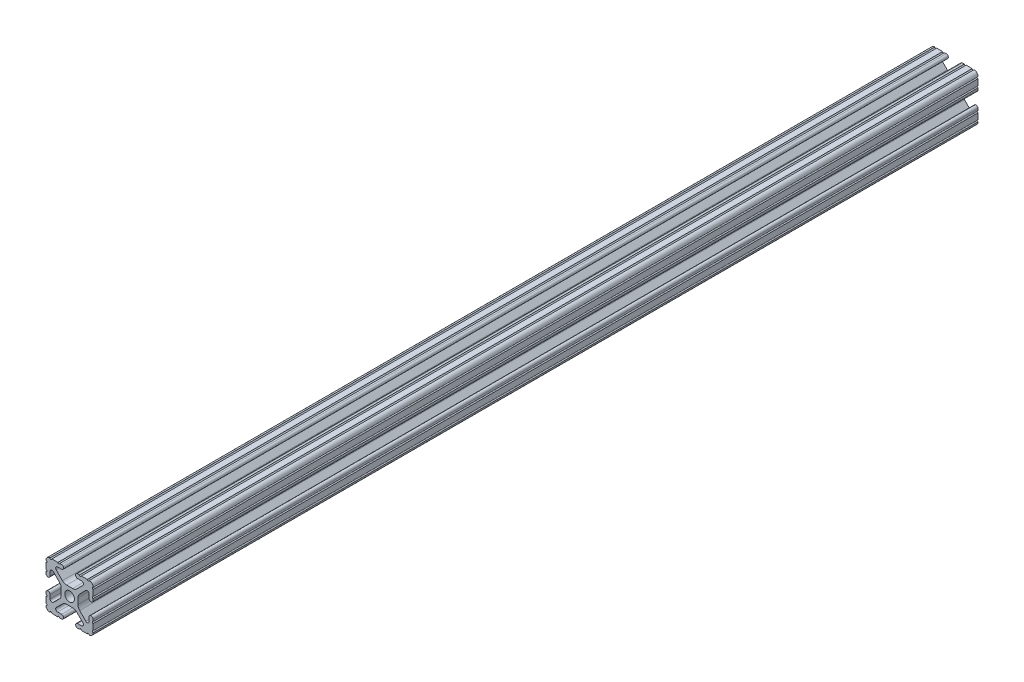
SolidWorks part; units mm, degrees
material "6061-T6 (SS)"
ref_plane "Front Plane" through (0, 0, 0) normal (0, 0, 1) x (1, 0, 0)
ref_plane "Top Plane" through (0, 0, 0) normal (0, 1, 0) x (1, 0, 0)
ref_plane "Right Plane" through (0, 0, 0) normal (1, 0, 0) x (0, 0, -1)
ref_plane "Plane1" through (0, 0, -450.85) normal (0, 0, -1) x (-1, 0, 0)
sketch "Sketch1" plane through (0, 0, -450.85) normal (0, 0, -1) x (-1, 0, 0)
  line L0 (12.7, -9.5504) -> (12.7, -6.3331)
  line L1 (12.7, -5.3171) -> (12.7, -4.3434)
  line L2 (10.4902, -4.3434) -> (10.4902, -6.4748)
  line L3 (8.7558, -7.1932) -> (5.4257, -3.8632)
  line L4 (4.4958, -1.6181) -> (4.4958, 1.6181)
  line L5 (5.4257, 3.8632) -> (8.7558, 7.1932)
  line L6 (10.4902, 6.4748) -> (10.4902, 4.3434)
  line L7 (12.7, 4.3434) -> (12.7, 5.3171)
  line L8 (12.7, 6.3331) -> (12.7, 9.5504)
  line L9 (9.5504, 12.7) -> (6.3331, 12.7)
  line L10 (5.3171, 12.7) -> (4.3434, 12.7)
  line L11 (4.3434, 10.4902) -> (6.4748, 10.4902)
  line L12 (7.1932, 8.7558) -> (3.8632, 5.4257)
  line L13 (1.6181, 4.4958) -> (-1.6181, 4.4958)
  line L14 (-3.8632, 5.4257) -> (-7.1932, 8.7558)
  line L15 (-6.4748, 10.4902) -> (-4.3434, 10.4902)
  line L16 (-4.3434, 12.7) -> (-5.3171, 12.7)
  line L17 (-6.3331, 12.7) -> (-9.5504, 12.7)
  line L18 (-12.7, 9.5504) -> (-12.7, 6.3331)
  line L19 (-12.7, 5.3171) -> (-12.7, 4.3434)
  line L20 (-10.4902, 4.3434) -> (-10.4902, 6.4748)
  line L21 (-8.7558, 7.1932) -> (-5.4257, 3.8632)
  line L22 (-4.4958, 1.6181) -> (-4.4958, -1.6181)
  line L23 (-5.4257, -3.8632) -> (-8.7558, -7.1932)
  line L24 (-10.4902, -6.4748) -> (-10.4902, -4.3434)
  line L25 (-12.7, -4.3434) -> (-12.7, -5.3171)
  line L26 (-12.7, -6.3331) -> (-12.7, -9.5504)
  line L27 (-9.5504, -12.7) -> (-6.3331, -12.7)
  line L28 (-5.3171, -12.7) -> (-4.3434, -12.7)
  line L29 (-4.3434, -10.4902) -> (-6.4748, -10.4902)
  line L30 (-7.1932, -8.7558) -> (-3.8632, -5.4257)
  line L31 (-1.6181, -4.4958) -> (1.6181, -4.4958)
  line L32 (3.8632, -5.4257) -> (7.1932, -8.7558)
  line L33 (6.4748, -10.4902) -> (4.3434, -10.4902)
  line L34 (4.3434, -12.7) -> (5.3171, -12.7)
  line L35 (6.3331, -12.7) -> (9.5504, -12.7)
  arc A0 (12.6998, -10.5664) -> (12.7, -9.5504) centre (12.7, -10.0584) cw
  arc A1 (12.7, -6.3331) -> (12.7, -5.3171) centre (12.7, -5.8251) cw
  arc A2 (12.7, -4.3434) -> (10.4902, -4.3434) centre (11.5951, -4.3434) ccw
  arc A3 (10.4902, -6.4748) -> (8.7558, -7.1932) centre (9.4742, -6.4748) cw
  arc A4 (5.4257, -3.8632) -> (4.4958, -1.6181) centre (7.6708, -1.6181) cw
  arc A5 (4.4958, 1.6181) -> (5.4257, 3.8632) centre (7.6708, 1.6181) cw
  arc A6 (8.7558, 7.1932) -> (10.4902, 6.4748) centre (9.4742, 6.4748) cw
  arc A7 (10.4902, 4.3434) -> (12.7, 4.3434) centre (11.5951, 4.3434) ccw
  arc A8 (12.7, 5.3171) -> (12.7, 6.3331) centre (12.7, 5.8251) cw
  arc A9 (12.7, 9.5504) -> (12.6998, 10.5664) centre (12.7, 10.0584) cw
  arc A10 (12.6998, 10.5664) -> (10.5664, 12.6998) centre (10.5918, 10.5918) ccw
  arc A11 (10.5664, 12.6998) -> (9.5504, 12.7) centre (10.0584, 12.7) cw
  arc A12 (6.3331, 12.7) -> (5.3171, 12.7) centre (5.8251, 12.7) cw
  arc A13 (4.3434, 12.7) -> (4.3434, 10.4902) centre (4.3434, 11.5951) ccw
  arc A14 (6.4748, 10.4902) -> (7.1932, 8.7558) centre (6.4748, 9.4742) cw
  arc A15 (3.8632, 5.4257) -> (1.6181, 4.4958) centre (1.6181, 7.6708) cw
  arc A16 (-1.6181, 4.4958) -> (-3.8632, 5.4257) centre (-1.6181, 7.6708) cw
  arc A17 (-7.1932, 8.7558) -> (-6.4748, 10.4902) centre (-6.4748, 9.4742) cw
  arc A18 (-4.3434, 10.4902) -> (-4.3434, 12.7) centre (-4.3434, 11.5951) ccw
  arc A19 (-5.3171, 12.7) -> (-6.3331, 12.7) centre (-5.8251, 12.7) cw
  arc A20 (-9.5504, 12.7) -> (-10.5664, 12.6998) centre (-10.0584, 12.7) cw
  arc A21 (-10.5664, 12.6998) -> (-12.6998, 10.5664) centre (-10.5918, 10.5918) ccw
  arc A22 (-12.6998, 10.5664) -> (-12.7, 9.5504) centre (-12.7, 10.0584) cw
  arc A23 (-12.7, 6.3331) -> (-12.7, 5.3171) centre (-12.7, 5.8251) cw
  arc A24 (-12.7, 4.3434) -> (-10.4902, 4.3434) centre (-11.5951, 4.3434) ccw
  arc A25 (-10.4902, 6.4748) -> (-8.7558, 7.1932) centre (-9.4742, 6.4748) cw
  arc A26 (-5.4257, 3.8632) -> (-4.4958, 1.6181) centre (-7.6708, 1.6181) cw
  arc A27 (-4.4958, -1.6181) -> (-5.4257, -3.8632) centre (-7.6708, -1.6181) cw
  arc A28 (-8.7558, -7.1932) -> (-10.4902, -6.4748) centre (-9.4742, -6.4748) cw
  arc A29 (-10.4902, -4.3434) -> (-12.7, -4.3434) centre (-11.5951, -4.3434) ccw
  arc A30 (-12.7, -5.3171) -> (-12.7, -6.3331) centre (-12.7, -5.8251) cw
  arc A31 (-12.7, -9.5504) -> (-12.6998, -10.5664) centre (-12.7, -10.0584) cw
  arc A32 (-12.6998, -10.5664) -> (-10.5664, -12.6998) centre (-10.5918, -10.5918) ccw
  arc A33 (-10.5664, -12.6998) -> (-9.5504, -12.7) centre (-10.0584, -12.7) cw
  arc A34 (-6.3331, -12.7) -> (-5.3171, -12.7) centre (-5.8251, -12.7) cw
  arc A35 (-4.3434, -12.7) -> (-4.3434, -10.4902) centre (-4.3434, -11.5951) ccw
  arc A36 (-6.4748, -10.4902) -> (-7.1932, -8.7558) centre (-6.4748, -9.4742) cw
  arc A37 (-3.8632, -5.4257) -> (-1.6181, -4.4958) centre (-1.6181, -7.6708) cw
  arc A38 (1.6181, -4.4958) -> (3.8632, -5.4257) centre (1.6181, -7.6708) cw
  arc A39 (7.1932, -8.7558) -> (6.4748, -10.4902) centre (6.4748, -9.4742) cw
  arc A40 (4.3434, -10.4902) -> (4.3434, -12.7) centre (4.3434, -11.5951) ccw
  arc A41 (5.3171, -12.7) -> (6.3331, -12.7) centre (5.8251, -12.7) cw
  arc A42 (9.5504, -12.7) -> (10.5664, -12.6998) centre (10.0584, -12.7) cw
  arc A43 (10.5664, -12.6998) -> (12.6998, -10.5664) centre (10.5918, -10.5918) ccw
  circle A44 centre (0, 0) radius 2.6035
extrude "Boss-Extrude1" add sketch "Sketch1" against normal mid plane 476.25
ref_plane "Plane2" through (0, 0, -450.85) normal (0, 0, 1) x (1, 0, 0)
